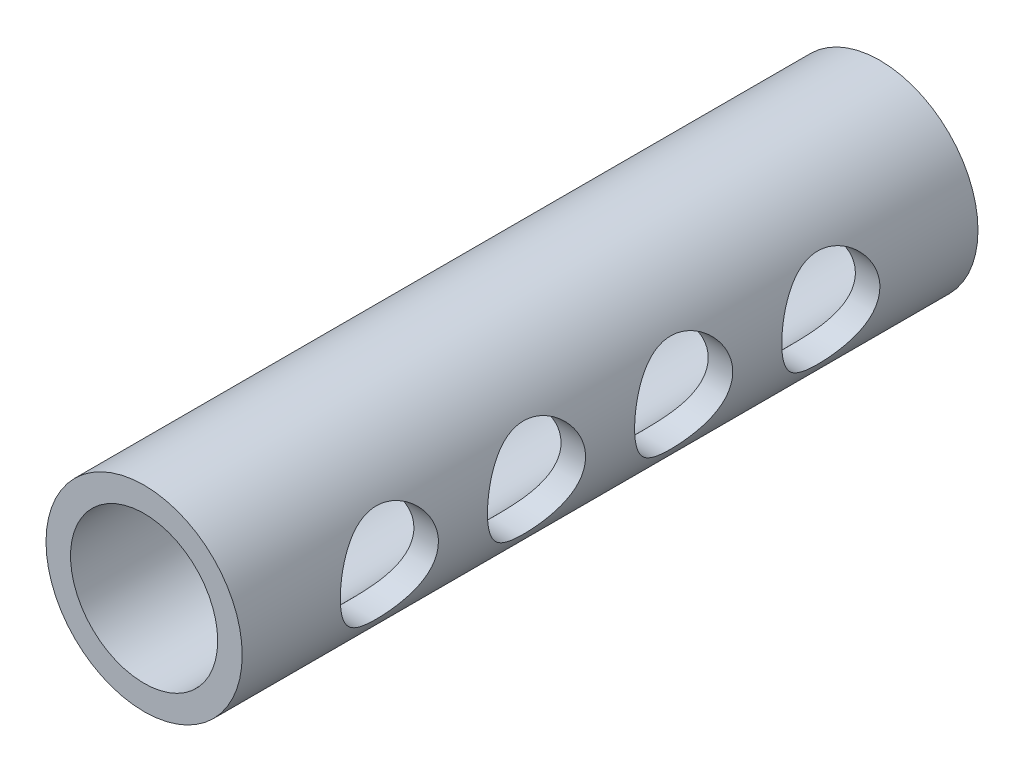
SolidWorks part; units mm, degrees
ref_plane "Front Plane" through (0, 0, 0) normal (0, 0, 1) x (1, 0, 0)
ref_plane "Top Plane" through (0, 0, 0) normal (0, 1, 0) x (1, 0, 0)
ref_plane "Right Plane" through (0, 0, 0) normal (1, 0, 0) x (0, 0, -1)
sketch "Sketch1" plane through (0, 0, 0) normal (0, 0, 1) x (1, 0, 0)
  circle A0 centre (0, 0) radius 4
  dimension "D1" = 8
extrude "Boss-Extrude1" add sketch "Sketch1" along normal blind 30
sketch "Sketch2" plane through (0, 0, 30) normal (0, 0, 1) x (1, 0, 0)
  circle A0 centre (0, 0) radius 3
extrude "Cut-Extrude1" cut sketch "Sketch2" against normal through all
sketch "Sketch3" plane through (0, 0, 0) normal (1, 0, 0) x (0, 0, -1)
  line L0 (-20.2102, 0) -> (2.9398, 0) construction
  line L2 (-30, 4) -> (-30, -4) construction
  line L3 (0, -4) -> (0, 4) construction
  circle A3 centre (-6, 0) radius 2
  circle A11 centre (-12, 0) radius 2
  circle A12 centre (-18, 0) radius 2
  circle A13 centre (-24, 0) radius 2
  dimension "D1" = 4
  dimension "D4" = 6
  dimension "D3" = 6
  dimension "D5" = 6
  dimension "D2" = 4
extrude "Cut-Extrude2" cut sketch "Sketch3" against normal blind 4 from offset 5
